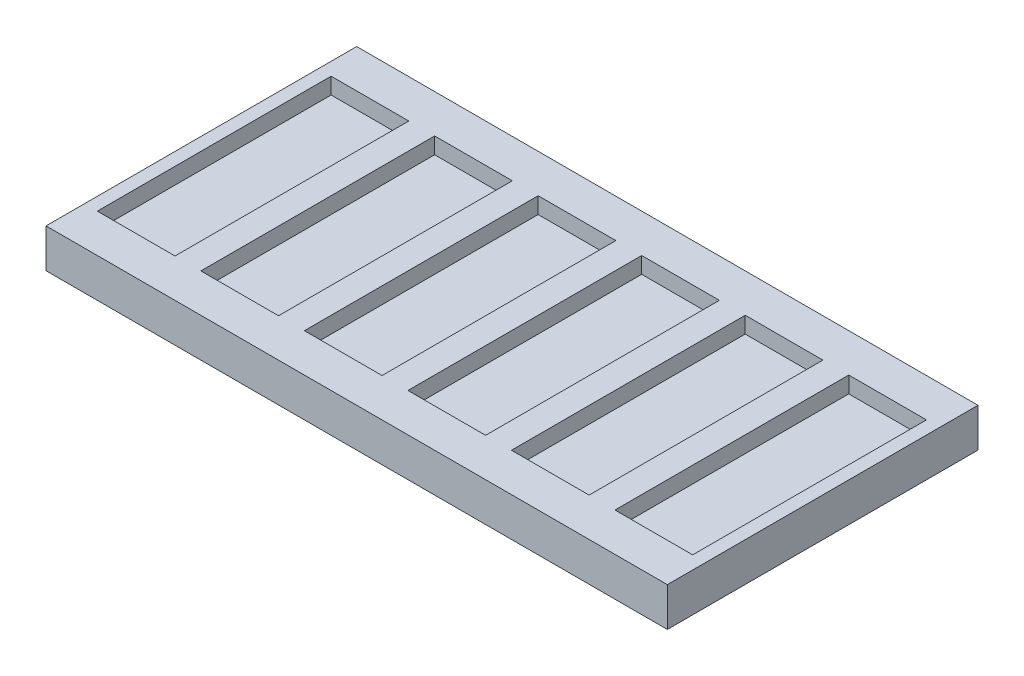
SolidWorks part; units mm, degrees
ref_plane "Спереди" through (0, 0, 0) normal (0, 0, 1) x (1, 0, 0)
ref_plane "Сверху" through (0, 0, 0) normal (0, 1, 0) x (1, 0, 0)
ref_plane "Справа" through (0, 0, 0) normal (1, 0, 0) x (0, 0, -1)
sketch "Эскиз1" plane through (0, 0, 0) normal (0, 1, 0) x (1, 0, 0)
  line L1 (40, -20) -> (-40, -20)
  line L2 (40, -20) -> (40, 20)
  line L3 (40, 20) -> (-40, 20)
  line L4 (-40, -20) -> (-40, 20)
  line L5 (40, -20) -> (-40, 20) construction
  line L6 (40, 20) -> (-40, -20) construction
  point P0 (0, 0)
  dimension "D1" = 40
  dimension "D2" = 80
extrude "Бобышка-Вытянуть1" add sketch "Эскиз1" along normal blind 5
sketch "Эскиз2" plane through (0, 5, 0) normal (0, 1, 0) x (1, 0, 0)
  line L0 (-40, 20) -> (-40, -20) construction
  line L1 (-38.34, 15.05) -> (-28.34, 15.05)
  line L2 (-38.34, 15.05) -> (-38.34, -15.05)
  line L3 (-38.34, -15.05) -> (-28.34, -15.05)
  line L4 (-28.34, 15.05) -> (-28.34, -15.05)
  line L5 (-40, -20) -> (40, -20) construction
  dimension "D1" = 10
  dimension "D2" = 1.66
  dimension "D3" = 30.1
  dimension "D4" = 4.95
extrude "Вырез-Вытянуть1" cut sketch "Эскиз2" against normal blind 2.1
pattern_linear "Линейный массив1" count 6 spacing 13.33 along (1, 0, 0) of "Вырез-Вытянуть1"
sketch "Эскиз3" plane through (-40, 0, 0) normal (-1, 0, 0) x (0, 0, 1)
  line L0 (-13.07, 0) -> (-13.07, -2)
  line L1 (-20, 0) -> (20, 0) construction
  line L2 (-13.07, -2) -> (-15.45, -2)
  line L3 (-15.45, -2) -> (-15.45, -3.44)
  line L4 (-15.45, -3.44) -> (-12.79, -6.1)
  line L5 (-12.79, -6.1) -> (-7.21, -6.1)
  line L6 (-7.21, -6.1) -> (-4.55, -3.44)
  line L7 (-4.55, -3.44) -> (-4.55, -2)
  line L8 (-4.55, -2) -> (-7.02, -2)
  line L9 (-7.02, -2) -> (-7.02, 0)
  line L10 (-7.02, 0) -> (-13.07, 0)
  line L11 (-20, 5) -> (-20, 0) construction
  line L12 (0, -2.75) -> (0, 2.75) construction
  line L13 (7.02, 0) -> (13.07, 0)
  line L14 (7.02, -2) -> (7.02, 0)
  line L15 (4.55, -2) -> (7.02, -2)
  line L16 (4.55, -3.44) -> (4.55, -2)
  line L17 (7.21, -6.1) -> (4.55, -3.44)
  line L18 (12.79, -6.1) -> (7.21, -6.1)
  line L19 (15.45, -3.44) -> (12.79, -6.1)
  line L20 (15.45, -2) -> (15.45, -3.44)
  line L21 (13.07, -2) -> (15.45, -2)
  line L22 (13.07, 0) -> (13.07, -2)
  dimension "D1" = 6.05
  dimension "D2" = 5.58
  dimension "D3" = 10.9
  dimension "D4" = 4.55
  dimension "D5" = 2.38
  dimension "D6" = 2.47
  dimension "D7" = 2.66
  dimension "D8" = 4.1
  dimension "D9" = 2
  dimension "D10" = 1.44
  dimension "D11" = 1.44
  dimension "D12" = 2
extrude "Бобышка-Вытянуть2" add sketch "Эскиз3" against normal up to surface (80 mm away) up to face at (40, 2.5, 0)
chamfer "Фаска1" distance 6.1 angle 45 4 edges at (40, -6.1, 10) (-40, -6.1, 10) (40, -6.1, -10) (-40, -6.1, -10)
